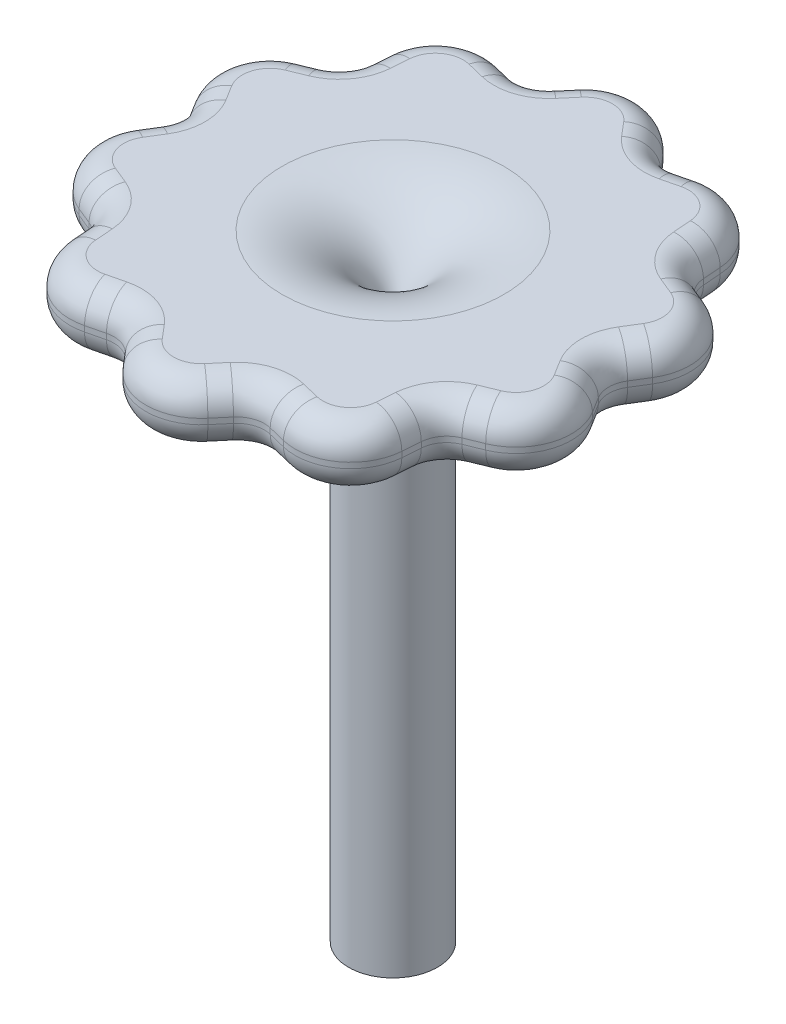
SolidWorks part; units mm, degrees
ref_plane "Front Plane" through (0, 0, 0) normal (0, 0, 1) x (1, 0, 0)
ref_plane "Top Plane" through (0, 0, 0) normal (0, 1, 0) x (1, 0, 0)
ref_plane "Right Plane" through (0, 0, 0) normal (1, 0, 0) x (0, 0, -1)
sketch "Sketch1" plane through (0, 0, 0) normal (0, 0, 1) x (1, 0, 0)
  line L0 (0, 0) -> (0, 91) construction
  line L1 (0, 0) -> (8, 0)
  line L2 (8, 0) -> (8, 80)
  line L3 (28, 100) -> (45, 100)
  line L4 (50, 105) -> (50, 106)
  line L5 (45, 111) -> (20, 111)
  line L6 (0, 0) -> (0, 91)
  arc A0 (8, 80) -> (28, 100) centre (28, 80) cw
  arc A1 (0, 91) -> (20, 111) centre (20, 91) cw
  arc A2 (45, 100) -> (50, 105) centre (45, 105) ccw
  arc A3 (50, 106) -> (45, 111) centre (45, 106) ccw
  point P10 (8, 100)
  dimension "D3" = 20
  dimension "D1" = 20
  dimension "D7" = 5
  dimension "D2" = 100
  dimension "D4" = 100
  dimension "D5" = 16
  dimension "D6" = 11
revolve "Revolve1" add sketch "Sketch1" angle 360 about L0
sketch "Sketch2" plane through (0, 111, 0) normal (0, 1, 0) x (1, 0, 0)
  line L0 (0, -50) -> (0, 0) construction
  line L1 (-29.3893, -40.4508) -> (0, 0) construction
  line L2 (-47.5528, -15.4508) -> (0, 0) construction
  line L3 (-47.5528, 15.4508) -> (0, 0) construction
  line L4 (-29.3893, 40.4508) -> (0, 0) construction
  line L5 (0, 50) -> (0, 0) construction
  line L6 (29.3893, 40.4508) -> (0, 0) construction
  line L7 (47.5528, 15.4508) -> (0, 0) construction
  line L8 (47.5528, -15.4508) -> (0, 0) construction
  line L9 (29.3893, -40.4508) -> (0, 0) construction
  line L10 (-29.3893, -40.4508) -> (-30.7426, -22.3358)
  line L11 (-30.7426, -22.3358) -> (-47.5528, -15.4508)
  line L12 (-47.5528, -15.4508) -> (-38, 0)
  line L13 (-38, 0) -> (-47.5528, 15.4508)
  line L14 (-47.5528, 15.4508) -> (-30.7426, 22.3358)
  line L15 (-30.7426, 22.3358) -> (-29.3893, 40.4508)
  line L16 (-29.3893, 40.4508) -> (-11.7426, 36.1401)
  line L17 (-11.7426, 36.1401) -> (0, 50)
  line L18 (0, 50) -> (11.7426, 36.1401)
  line L19 (11.7426, 36.1401) -> (29.3893, 40.4508)
  line L20 (29.3893, 40.4508) -> (30.7426, 22.3358)
  line L21 (30.7426, 22.3358) -> (47.5528, 15.4508)
  line L22 (47.5528, 15.4508) -> (38, 0)
  line L23 (38, 0) -> (47.5528, -15.4508)
  line L24 (47.5528, -15.4508) -> (30.7426, -22.3358)
  line L25 (30.7426, -22.3358) -> (29.3893, -40.4508)
  line L26 (29.3893, -40.4508) -> (11.7426, -36.1401)
  line L27 (11.7426, -36.1401) -> (0, -50)
  line L28 (0, -50) -> (-11.7426, -36.1401)
  line L29 (-11.7426, -36.1401) -> (-29.3893, -40.4508)
  line L30 (-30.7426, -22.3358) -> (0, 0) construction
  circle A2 centre (0, 0) radius 50 construction
  point P25 (0, 0)
  dimension "D1" = 10
extrude "Extrude1" cut sketch "Sketch2" against normal blind 40 flip side to cut
fillet "Congé1" radius 10 7 edges at (-42.7975, 100, 13.9058) (-42.7975, 111, 13.9058) (-47.5528, 105.5, 15.4508) (-46.6913, 108.5626, 15.8037) (-46.0124, 101.6836, 16.0817) (-46.6775, 109.3164, 14.035) (-47.0632, 102.4374, 14.659)
fillet "Congé2" radius 10 7 edges at (-26.4503, 100, 36.4058) (-26.4503, 111, 36.4058) (-29.3893, 105.5, 40.4508) (-28.4849, 108.5626, 40.2299) (-27.7722, 101.6836, 40.0558) (-29.5133, 109.3164, 38.7909) (-29.4586, 102.4374, 39.5225)
fillet "Congé3" radius 10 7 edges at (0, 105.5, 50) (0.6018, 108.5626, 49.2897) (1.076, 101.6836, 48.73) (0, 100, 45) (0, 111, 45) (-1.076, 109.3164, 48.73) (-0.6018, 102.4374, 49.2897)
fillet "Congé4" radius 10 7 edges at (29.3893, 105.5, 40.4508) (29.4586, 108.5626, 39.5225) (29.5133, 101.6836, 38.7909) (27.7722, 109.3164, 40.0558) (28.4849, 102.4374, 40.2299) (26.4503, 100, 36.4058) (26.4503, 111, 36.4058)
fillet "Congé5" radius 10 7 edges at (47.5528, 105.5, 15.4508) (47.0632, 108.5626, 14.659) (46.6775, 101.6836, 14.035) (46.0124, 109.3164, 16.0817) (46.6913, 102.4374, 15.8037) (42.7975, 100, 13.9058) (42.7975, 111, 13.9058)
fillet "Congé6" radius 10 7 edges at (47.5528, 105.5, -15.4508) (46.6913, 108.5626, -15.8037) (46.0124, 101.6836, -16.0817) (46.6775, 109.3164, -14.035) (47.0632, 102.4374, -14.659) (42.7975, 100, -13.9058) (42.7975, 111, -13.9058)
fillet "Congé7" radius 10 7 edges at (29.3893, 105.5, -40.4508) (28.4849, 108.5626, -40.2299) (27.7722, 101.6836, -40.0558) (29.5133, 109.3164, -38.7909) (29.4586, 102.4374, -39.5225) (26.4503, 100, -36.4058) (26.4503, 111, -36.4058)
fillet "Congé8" radius 10 7 edges at (0, 105.5, -50) (-0.6018, 108.5626, -49.2897) (-1.076, 101.6836, -48.73) (1.076, 109.3164, -48.73) (0.6018, 102.4374, -49.2897) (0, 100, -45) (0, 111, -45)
fillet "Congé9" radius 10 7 edges at (-29.5133, 101.6836, -38.7909) (-27.7722, 109.3164, -40.0558) (-28.4849, 102.4374, -40.2299) (-26.4503, 100, -36.4058) (-26.4503, 111, -36.4058) (-29.3893, 105.5, -40.4508) (-29.4586, 108.5626, -39.5225)
fillet "Congé10" radius 10 7 edges at (-42.7975, 100, -13.9058) (-42.7975, 111, -13.9058) (-47.5528, 105.5, -15.4508) (-47.0632, 108.5626, -14.659) (-46.6775, 101.6836, -14.035) (-46.0124, 109.3164, -16.0817) (-46.6913, 102.4374, -15.8037)
fillet "Fillet1" radius 5 70 edges at (-9.6862, 100, 38.5674) (-9.6862, 111, 38.5674) (-14.833, 111, 36.8951) (-11.7426, 105.5, 36.1401) (-14.833, 100, 36.8951) (-30.5056, 100, 25.5082) (-30.5056, 111, 25.5082) (-33.6865, 111, 21.1301) (-30.7426, 105.5, 22.3358) (-33.6865, 100, 21.1301) (-39.6729, 100, 2.7058) (-39.6729, 111, 2.7058) (-39.6729, 111, -2.7058) (-38, 105.5, 0) (-39.6729, 100, -2.7058) (-33.6865, 100, -21.1301) (-33.6865, 111, -21.1301) (-30.5056, 111, -25.5082) (-30.7426, 105.5, -22.3358) (-30.5056, 100, -25.5082) (-14.833, 100, -36.8951) (-14.833, 111, -36.8951) (-9.6862, 111, -38.5674) (-11.7426, 105.5, -36.1401) (-9.6862, 100, -38.5674) (9.6862, 100, -38.5674) (9.6862, 111, -38.5674) (14.833, 111, -36.8951) (11.7426, 105.5, -36.1401) (14.833, 100, -36.8951) (30.5056, 100, -25.5082) (30.5056, 111, -25.5082) (33.6865, 111, -21.1301) (30.7426, 105.5, -22.3358) (33.6865, 100, -21.1301) (39.6729, 100, -2.7058) (39.6729, 111, -2.7058) (39.6729, 111, 2.7058) (38, 105.5, 0) (39.6729, 100, 2.7058) (33.6865, 100, 21.1301) (33.6865, 111, 21.1301) (30.5056, 111, 25.5082) (30.7426, 105.5, 22.3358) (30.5056, 100, 25.5082) (14.833, 100, 36.8951) (14.833, 111, 36.8951) (9.6862, 111, 38.5674) (11.7426, 105.5, 36.1401) (9.6862, 100, 38.5674) (-26.1743, 111, 36.0258) (-26.1743, 100, 36.0258) (-42.3509, 111, 13.7606) (-42.3509, 100, 13.7606) (-42.3509, 111, -13.7606) (-42.3509, 100, -13.7606) (-26.1743, 111, -36.0258) (-26.1743, 100, -36.0258) (0, 111, -44.5303) (0, 100, -44.5303) (26.1743, 111, -36.0258) (26.1743, 100, -36.0258) (42.3509, 111, -13.7606) (42.3509, 100, -13.7606) (42.3509, 111, 13.7606) (42.3509, 100, 13.7606) (26.1743, 111, 36.0258) (26.1743, 100, 36.0258) (0, 100, 44.5303) (0, 111, 44.5303)
